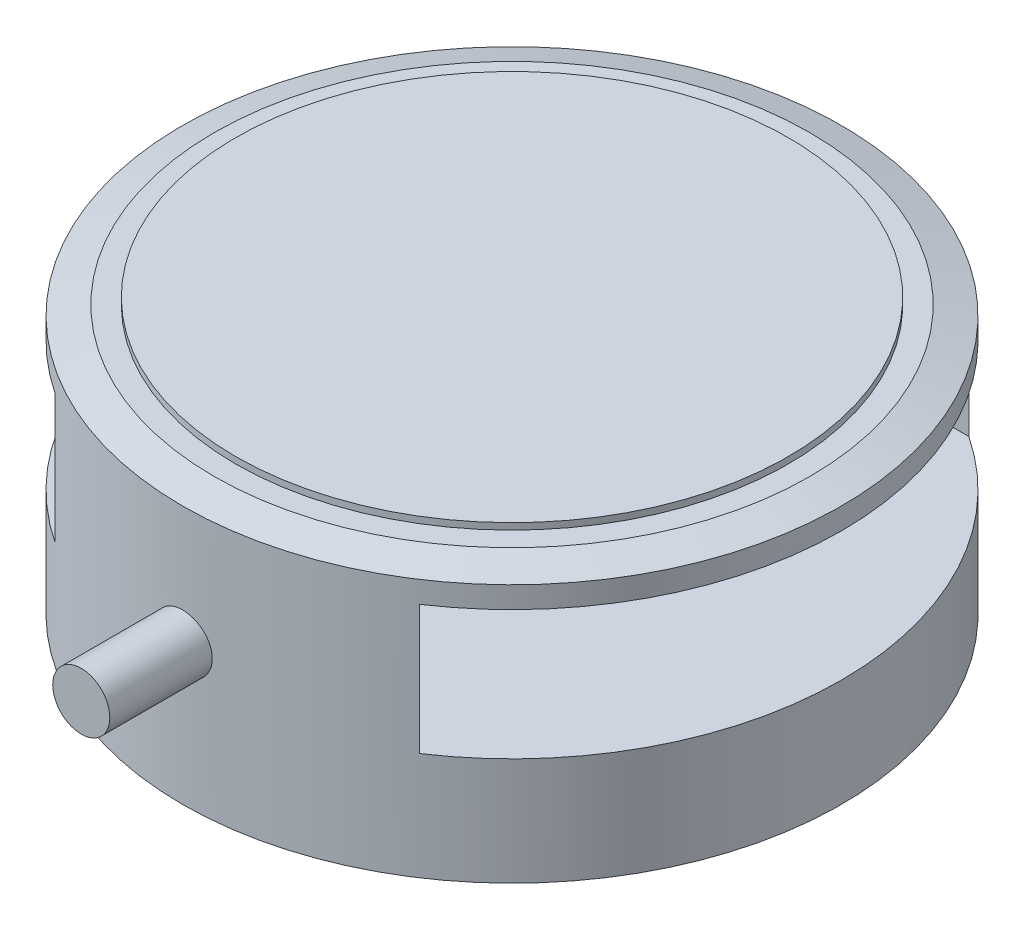
SolidWorks part; units mm, degrees
ref_plane "前视基准面" through (0, 0, 0) normal (0, 0, 1) x (1, 0, 0)
ref_plane "上视基准面" through (0, 0, 0) normal (0, 1, 0) x (1, 0, 0)
ref_plane "右视基准面" through (0, 0, 0) normal (1, 0, 0) x (0, 0, -1)
sketch "草图1" plane through (0, 0, 0) normal (0, 1, 0) x (1, 0, 0)
  circle A0 centre (0, 0) radius 30.6
  dimension "D1" = 61.2
extrude "凸台-拉伸1" add sketch "草图1" along normal blind 24
sketch "草图2" plane through (0, 24, 0) normal (0, 1, 0) x (1, 0, 0)
  circle A1 centre (0, 0) radius 30.6
  circle A2 centre (0, 0) radius 30.6
  dimension "D1" = 0
sketch "草图3" plane through (0, 24, 0) normal (0, 1, 0) x (1, 0, 0)
  circle A1 centre (0, 0) radius 30.6
  circle A2 centre (0, 0) radius 30.6
  dimension "D1" = 0
extrude "凸台-拉伸2" add sketch "草图3" along normal blind 0.9 draft 73
sketch "草图4" plane through (0, 24.9, 0) normal (0, 1, 0) x (1, 0, 0)
  circle A2 centre (0, 0) radius 25.6562
  circle A3 centre (0, 0) radius 25.6562
  dimension "D1" = 2
extrude "凸台-拉伸3" add sketch "草图4" along normal blind 0.6
sketch "草图5" plane through (0, 0, 0) normal (1, 0, 0) x (0, 0, -1)
  line L0 (0, 0) -> (0, 50000) construction
  line L1 (-30.6, 0) -> (30.6, 0) construction
  line L2 (-25.5, 10) -> (25.5, 10)
  line L3 (25.5, 10) -> (25.5, 22)
  line L4 (25.5, 22) -> (-25.5, 22)
  line L5 (-25.5, 22) -> (-25.5, 10)
  point P4 (0, 0)
  point P8 (0, 10)
  dimension "D1" = 10
  dimension "D2" = 12
  dimension "D3" = 51
extrude "切除-拉伸1" cut sketch "草图5" against normal through all and the other way through all
ref_plane "基准面1" through (0, 0, 27) normal (0, 0, 1) x (1, 0, 0)
sketch "草图6" plane through (0, 0, 27) normal (0, 0, 1) x (1, 0, 0)
  line L0 (0, 13) -> (0, -49987) construction
  circle A0 centre (0, 13) radius 2.65
  dimension "D1" = 5.3
  dimension "D2" = 13
extrude "凸台-拉伸4" add sketch "草图6" along normal blind 13
sketch "草图7" plane through (0, 0, 0) normal (0, -1, 0) x (1, 0, 0)
  circle A1 centre (0, 0) radius 30.6
  circle A2 centre (0, 0) radius 30.6 construction
  point P1 (0, 0)
  dimension "D1" = 0
